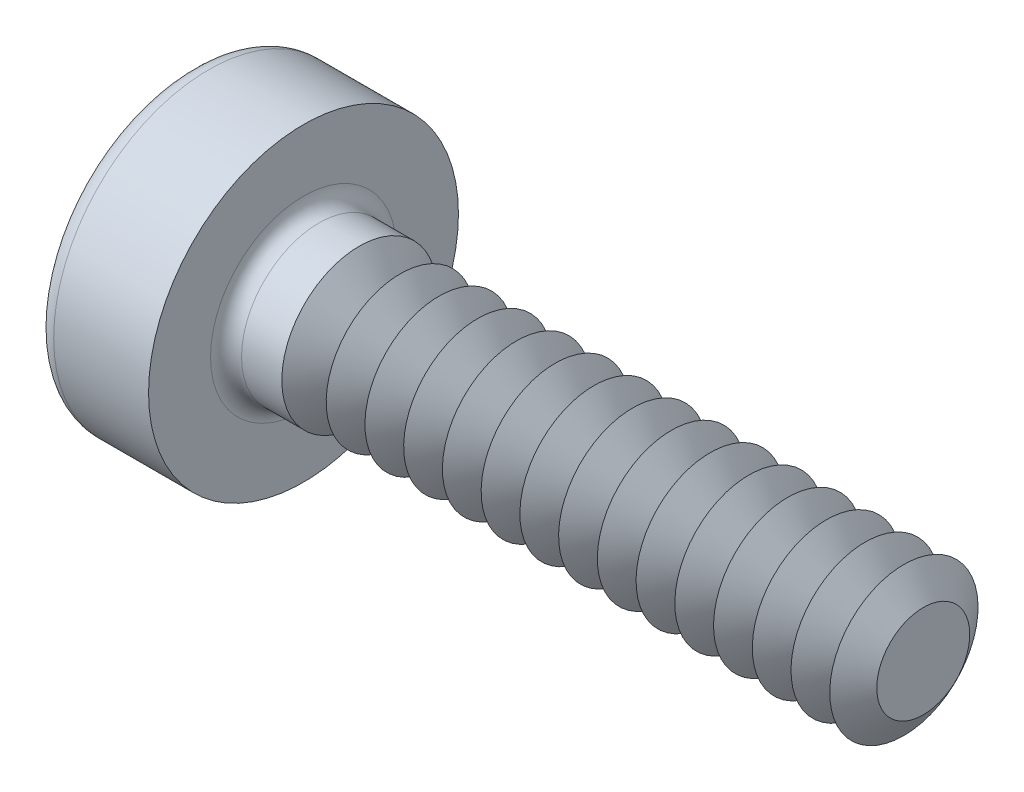
SolidWorks part; units mm, degrees
ref_plane "Plane1" through (0, 0, 0) normal (0, 0, 1) x (1, 0, 0)
ref_plane "Plane2" through (0, 0, 0) normal (0, 1, 0) x (1, 0, 0)
ref_plane "Plane3" through (0, 0, 0) normal (1, 0, 0) x (0, 0, -1)
sketch "BodySke" plane through (0, 0, 0) normal (0, 0, 1) x (1, 0, 0)
  line L0 (1, 0.5) -> (1, 1)
  line L1 (1.125, 6.35) -> (1.125, -3.175) construction
  line L2 (-25.4, 0) -> (127, 0) construction
  line L3 (5, 0) -> (0, 0)
  line L4 (1, 0.5) -> (5, 0.5)
  line L5 (5, 0.5) -> (5, 0)
  line L6 (0.3878, 1) -> (1, 1)
  line L8 (1, 6.35) -> (1, -3.175) construction
  arc A0 (0.2881, 0.9468) -> (0, 0) centre (1.7, 0) ccw
  arc A2 (0.2881, 0.9468) -> (0.3878, 1) centre (0.3878, 0.88) cw
  dimension "Head_crown_rad" = 1.7
  dimension "Head_fillet_rad" = 0.12
  dimension "Length" = 4
  dimension "Head_ht" = 1
  dimension "Head_dia" = 2
  dimension "Advance" = 0.25
  dimension "Thread_nom" = 4
  dimension "Diameter" = 1
revolve "Base-Revolve" add sketch "BodySke" angle 360 about L2
cosmetic thread "ThreadCosmetic" [suppressed] parameters "Thread_length"=3.5, "Thread_minor"=0.6
fillet "Fillet1" radius 0.1 1 edges at (1, 0, 0.5)
sketch "Sketch3" plane through (0, 0, 0) normal (1, 0, 0) x (0, 0, -1)
  line L0 (0.24, -0.8) -> (-0.24, -0.8)
  line L1 (0.24, -0.8) -> (0.24, 0.8)
  line L2 (-0.24, 0.8) -> (0.24, 0.8)
  line L3 (-0.24, 0.8) -> (-0.24, -0.8)
  dimension "Cross_dia" = 1.6
  dimension "D1" = 0.8
  dimension "Cross_width" = 0.48
  dimension "D2" = 0.24
ref_plane "Plane4" through (0.5, 0, 0) normal (1, 0, 0) x (0, 0, -1)
sketch "Sketch4" plane through (0.5, 0, 0) normal (1, 0, 0) x (0, 0, -1)
  line L0 (0.24, -0.5507) -> (-0.24, -0.5507)
  line L1 (0.24, -0.5507) -> (0.24, 0.5507)
  line L2 (-0.24, 0.5507) -> (0.24, 0.5507)
  line L3 (-0.24, 0.5507) -> (-0.24, -0.5507)
  dimension "D1" = 0.48
  dimension "D2" = 1.1014
  dimension "D3" = 0.24
  dimension "D4" = 0.5507
loft "Recess" cut profiles "Sketch3", "Sketch4"
pattern_circular "RecPat" count 2 every 90 about axis through (0, 0, 0) along (1, 0, 0) of "Recess"
sketch "RecCorSke" plane through (0, 0, 0) normal (0, 0, 1) x (1, 0, 0)
  line L0 (-3.175, 0) -> (15.875, 0) construction
  line L1 (-25.4, 0) -> (127, 0) construction
  line L2 (0, 0) -> (0, 0.3905)
  line L3 (0, 0.3905) -> (0.5, 0.3555)
  line L4 (0.5, 0.3555) -> (0.6155, 0)
  line L5 (0.6155, 0) -> (0, 0)
  dimension "Diameter" = 0.711
  dimension "Depth" = 0.5
  dimension "Draft_angle" = 4
  dimension "Bottom_angle" = 18
revolve "RecessCore" cut sketch "RecCorSke" angle 360 about L0
sketch "ThdSchSke" plane through (0, 0, 0) normal (0, 0, 1) x (1, 0, 0)
  line L0 (1.5, -0.3) -> (1.36, -0.5)
  line L1 (1.5, -0.3) -> (1.64, -0.5)
  line L2 (1.64, -0.5) -> (1.64, -0.625)
  line L3 (-3.175, 0) -> (5.1513, 0) construction
  line L5 (1.64, -0.625) -> (1.36, -0.625)
  line L6 (1.36, -0.625) -> (1.36, -0.5)
  dimension "Diameter" = 1
  dimension "SideAngle" = 55
  dimension "VeeAngle" = 70
  dimension "Thread_minor" = 0.6
  dimension "Overcut" = 1.25
  dimension "Start" = 1.5
revolve "ThreadSchematic" cut sketch "ThdSchSke" angle 360 about L3
pattern_linear "ThdSchPat" count 15 spacing 0.25 along (1, 0, 0) of "ThreadSchematic"
equation "\"D1@Sketch3\" = \"Cross_dia@Sketch3\" / 2"
equation "\"D2@Sketch3\" = \"Cross_width@Sketch3\" / 2"
equation "\"Depth@RecCorSke\" = \"Cross_depth@Plane4\""
equation "\"D1@Sketch4\" = \"Cross_width@Sketch3\""
equation "\"D2@Sketch4\" = \"Cross_dia@Sketch3\" - 2.0 * \"Cross_depth@Plane4\" * tan(26.5  * 0.017453292)"
equation "\"D3@Sketch4\" = \"D1@Sketch4\" / 2"
equation "\"D4@Sketch4\" = \"D2@Sketch4\" / 2"
equation "\"Thread_length@ThreadCosmetic\" = ((sgn( (\"Length@BodySke\" - \"Advance@BodySke\" * 2.0 ) - \"Thread_nom@BodySke\" )-1)*( (\"Length@BodySke\" - \"Advance@BodySke\" * 2.0 ) - \"Thread_nom@BodySke\" ))/-2+ \"Thread_nom@BodySke\""
equation "\"Thread_minor@ThdSchSke\" = \"Thread_minor@ThreadCosmetic\""
equation "\"Diameter@ThdSchSke\" = \"Diameter@BodySke\""
equation "\"Overcut@ThdSchSke\" = \"Diameter@BodySke\" * 1.25"
equation "\"Start@ThdSchSke\" = \"Head_ht@BodySke\" + \"Length@BodySke\" - \"Thread_length@ThreadCosmetic\"  '---Non-countersunk---"
equation "\"Num_threads@ThdSchPat\" = int( \"Thread_length@ThreadCosmetic\" / \"Advance@BodySke\" + 0.999 )  + 1"
equation "\"Advance@ThdSchPat\" = \"Thread_length@ThreadCosmetic\" /  (\"Num_threads@ThdSchPat\" - 1) 'relax it"
